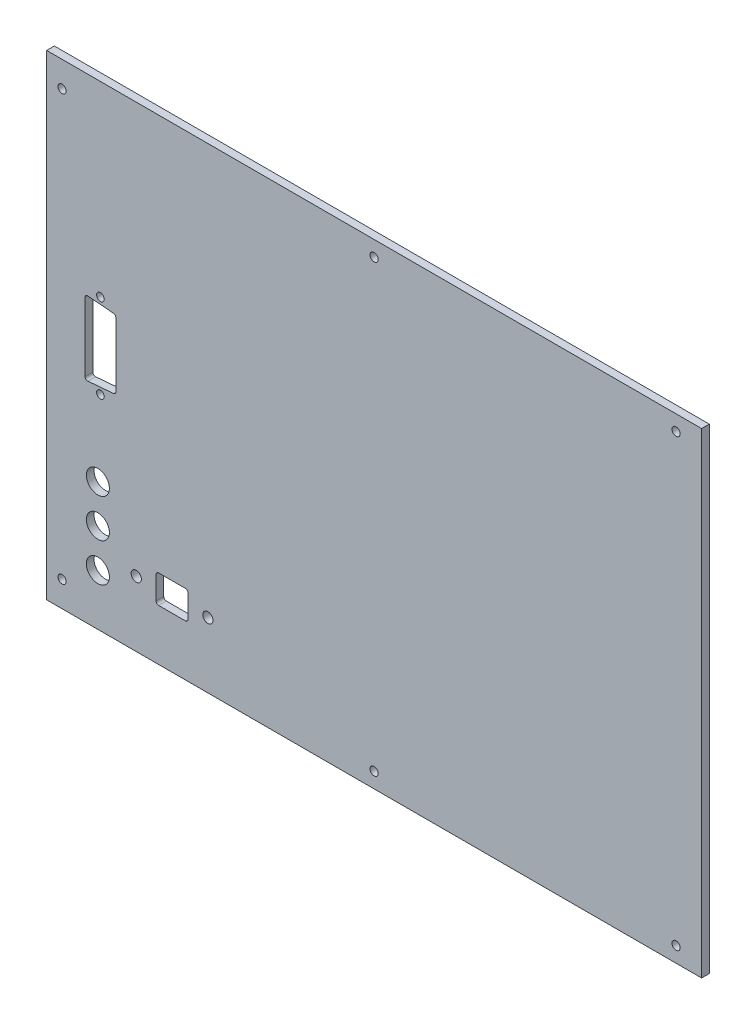
SolidWorks part; units mm, degrees
material "PMMA laser cult panels"
ref_plane "Front Plane" through (0, 0, 0) normal (0, 0, 1) x (1, 0, 0)
ref_plane "Top Plane" through (0, 0, 0) normal (0, 1, 0) x (1, 0, 0)
ref_plane "Right Plane" through (0, 0, 0) normal (1, 0, 0) x (0, 0, -1)
sketch "Sketch2" plane through (0, 0, 0) normal (0, 0, 1) x (1, 0, 0)
  line L1 (0, 0) -> (256, 0)
  line L2 (0, 0) -> (0, 186)
  line L3 (0, 186) -> (256, 186)
  line L4 (256, 0) -> (256, 186)
  dimension "D1" = 256
  dimension "D2" = 186
extrude "Boss-Extrude1" add sketch "Sketch2" along normal blind 3
sketch "Sketch3" plane through (0, 0, 3) normal (0, 0, 1) x (1, 0, 0)
  line L0 (256, 186) -> (0, 186) construction
  line L1 (0, 0) -> (256, 0) construction
  line L2 (0, 186) -> (0, 0) construction
  circle A0 centre (6, 176) radius 1.6
  circle A1 centre (128, 180) radius 1.6
  circle A2 centre (246, 180) radius 1.6
  circle A3 centre (246, 6) radius 1.6
  circle A4 centre (128, 6) radius 1.6
  circle A5 centre (6, 10) radius 1.6
  dimension "D8" = 3.2
  dimension "D1" = 10
  dimension "D2" = 6
  dimension "D3" = 10
  dimension "D4" = 6
  dimension "D5" = 6
  dimension "D6" = 128
  dimension "D7" = 246
extrude "Cut-Extrude1" cut sketch "Sketch3" against normal through all
sketch "Sketch4" plane through (0, 0, 3) normal (0, 0, 1) x (1, 0, 0)
  line L0 (0, 186) -> (0, 0) construction
  line L1 (42.75, 31) -> (55.25, 31)
  line L2 (42.75, 31) -> (42.75, 20)
  line L3 (42.75, 20) -> (55.25, 20)
  line L4 (55.25, 31) -> (55.25, 20)
  line L5 (0, 0) -> (256, 0) construction
  circle A0 centre (35, 25.5) radius 2
  circle A1 centre (63, 25.5) radius 2
  point P8 (49, 31)
  dimension "D6" = 4
  dimension "D7" = 4
  dimension "D1" = 12.5
  dimension "D2" = 11
  dimension "D3" = 14
  dimension "D4" = 5.5
  dimension "D5" = 28
  dimension "D8" = 35
  dimension "D9" = 20
extrude "Cut-Extrude2" cut sketch "Sketch4" against normal blind 10
fillet "Fillet1" radius 1 4 edges at (55.25, 31, 1.5) (55.25, 20, 1.5) (42.75, 31, 1.5) (42.75, 20, 1.5)
sketch "Sketch5" plane through (0, 0, 3) normal (0, 0, 1) x (1, 0, 0)
  line L0 (0, 0) -> (256, 0) construction
  line L1 (0, 186) -> (0, 0) construction
  circle A6 centre (20, 35) radius 4.5
  circle A7 centre (20, 20) radius 4.5
  circle A8 centre (20, 50) radius 4.5
  dimension "D2" = 15
  dimension "D3" = 0
  dimension "D4" = 9
  dimension "D5" = 9
  dimension "D7" = 9
  dimension "D6" = 20
  dimension "D8" = 20
  dimension "D9" = 15
extrude "Cut-Extrude3" cut sketch "Sketch5" against normal blind 10
sketch "Sketch7" plane through (161.9925, 0.2032, 3) normal (0, 0, 1) x (1, 0, 0)
  line L0 (-146.9925, 110.7968) -> (-146.9925, 81.7968)
  line L5 (-146.9925, 81.7968) -> (-134.9925, 82.7968)
  line L6 (-134.9925, 82.7968) -> (-134.9925, 109.7968)
  line L7 (-134.9925, 109.7968) -> (-146.9925, 110.7968)
  line L13 (-161.9925, 185.7968) -> (-161.9925, -0.2032) construction
  line L14 (-161.9925, -0.2032) -> (94.0075, -0.2032) construction
  circle A3 centre (-140.9925, 112.7968) radius 1.5
  circle A4 centre (-140.9925, 79.7968) radius 1.5
  point P20 (-146.9925, 96.2968)
  point P21 (-134.9925, 96.2968)
  dimension "D2" = 15
  dimension "D3" = 80
  dimension "D5" = 3
  dimension "D6" = 3
  dimension "D7" = 29
  dimension "D8" = 27
  dimension "D9" = 12
  dimension "D10" = 12
  dimension "D11" = 33
  dimension "D12" = 16.5
  dimension "D17" = 6
  dimension "D18" = 6
extrude "Cut-Extrude4" cut sketch "Sketch7" against normal through all
fillet "Fillet2" radius 1 4 edges at (27, 110, 1.5) (27, 83, 1.5) (15, 82, 1.5) (15, 111, 1.5)
